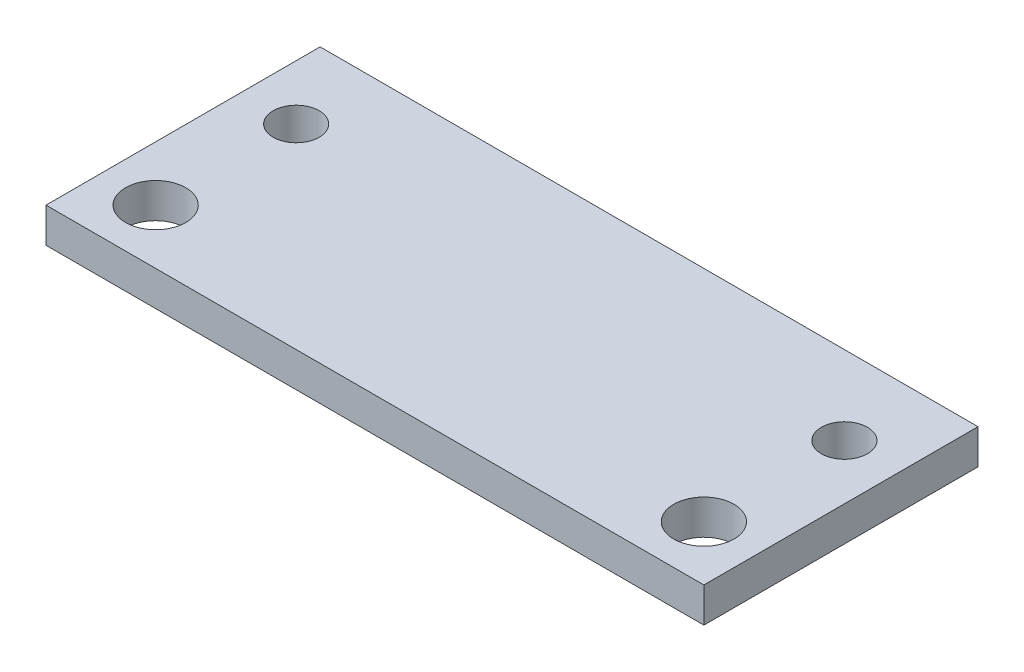
SolidWorks part; units mm, degrees
ref_plane "Front Plane" through (0, 0, 0) normal (0, 0, 1) x (1, 0, 0)
ref_plane "Top Plane" through (0, 0, 0) normal (0, 1, 0) x (1, 0, 0)
ref_plane "Right Plane" through (0, 0, 0) normal (1, 0, 0) x (0, 0, -1)
sketch "Sketch1" plane through (0, 0, 0) normal (0, 1, 0) x (1, 0, 0)
  line L0 (-60, 12.5) -> (0, 12.5) construction
  line L1 (0, 0) -> (-60, 0)
  line L2 (0, 0) -> (0, 25)
  line L3 (0, 25) -> (-60, 25)
  line L4 (-60, 0) -> (-60, 25)
  line L5 (-60, 5) -> (0, 5) construction
  point P9 (-55, 5)
  point P10 (-5, 5)
  point P11 (-5, 17.8156)
  point P12 (-55, 17.8156)
  point P13 (0, 0)
  point P14 (0, 0)
  point P15 (0, 0)
  dimension "D1" = 60
  dimension "D2" = 25
  dimension "D3" = 5
  dimension "D4" = 5
  dimension "D5" = 5
  dimension "D6" = 50
  dimension "D7" = 12.8156
extrude "Boss-Extrude1" add sketch "Sketch1" along normal blind 3.175
sketch "Sketch2" plane through (0, 3.175, 0) normal (0, 1, 0) x (1, 0, 0)
  point P0 (-55, 5)
  point P2 (-5, 5)
  point P4 (-5, 17.8156)
  point P6 (-55, 17.8156)
hole_wizard "M5 Clearance Hole2" positions "3DSketch3" profile "Sketch5" hole size "M5" standard "ANSI Metric"
sketch3d "3DSketch3"
  point P0 (-55, 3.175, -5)
  point P3 (-5, 3.175, -5)
sketch "Sketch5" plane through (-55, 3.175, -5) normal (1, 0, 0) x (0, 0, 1)
  line L0 (0, 0) -> (0, 16.6524)
  line L1 (0, 16.6524) -> (2.75, 15)
  line L2 (2.75, 15) -> (2.75, 0)
  line L5 (2.75, 0) -> (0, 0)
  line L10 (0, 16.6524) -> (-2.75, 15) construction
  line L11 (0, -6.35) -> (0, 107.95) construction
  dimension "Hole Dia." = 5.5
  dimension "Hole Depth" = 15
  dimension "Drill Angle" = 118
hole_wizard "M5x0.8 Tapped Hole2" positions "3DSketch5" profile "Sketch7" tap size "M5x0.8" standard "ANSI Metric"
sketch3d "3DSketch5"
  point P0 (-55, 3.175, -17.8156)
  point P3 (-5, 3.175, -17.8156)
sketch "Sketch7" plane through (-55, 3.175, -17.8156) normal (1, 0, 0) x (0, 0, 1)
  line L0 (0, 0) -> (0, 16.2618)
  line L1 (0, 16.2618) -> (2.1, 15)
  line L2 (2.1, 15) -> (2.1, 0)
  line L5 (2.1, 0) -> (0, 0)
  line L10 (0, 16.2618) -> (-2.1, 15) construction
  line L11 (0, -6.35) -> (0, 107.95) construction
  dimension "Tap Drill Dia." = 4.2
  dimension "Tap Drill Depth" = 15
  dimension "Drill Angle" = 118
cosmetic thread "Hole Thread1" parameters "D1"=10, "D2"=5.2
cosmetic thread "Hole Thread2" parameters "D1"=10, "D2"=5.2
